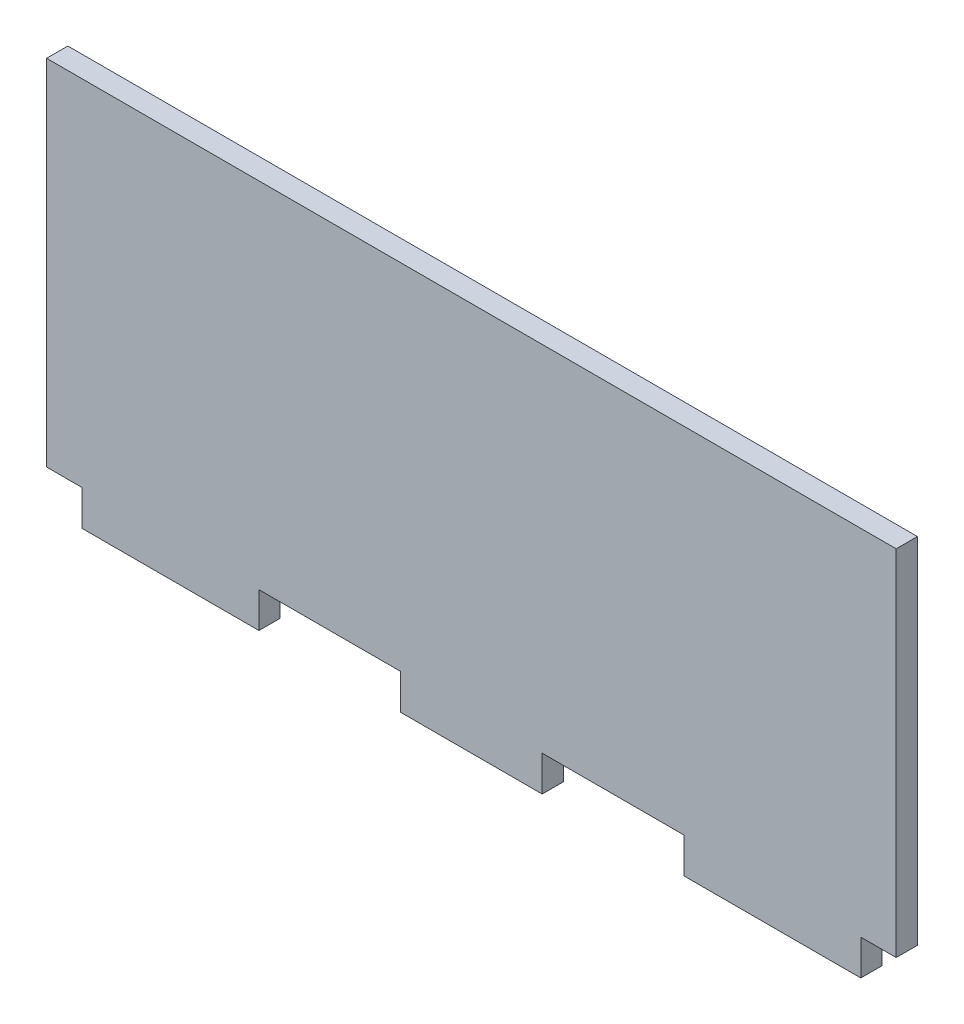
SolidWorks part; units mm, degrees
ref_plane "Plano frontal" through (0, 0, 0) normal (0, 0, 1) x (1, 0, 0)
ref_plane "Plano superior" through (0, 0, 0) normal (0, 1, 0) x (1, 0, 0)
ref_plane "Plano direito" through (0, 0, 0) normal (1, 0, 0) x (0, 0, -1)
sketch "Esboço1" plane through (0, 0, 0) normal (0, 0, 1) x (1, 0, 0)
  line L0 (-43.4908, -22.8963) -> (-23.4908, -22.8963)
  line L1 (-73.4908, 27.1037) -> (46.5092, 27.1037)
  line L2 (-73.4908, 27.1037) -> (-73.4908, -22.8963)
  line L3 (-73.4908, -22.8963) -> (-68.4908, -22.8963)
  line L4 (46.5092, 27.1037) -> (46.5092, -22.8963)
  line L5 (-3.4908, -22.8963) -> (16.5092, -22.8963)
  line L6 (-68.4908, -22.8963) -> (-68.4908, -27.8963)
  line L7 (-68.4908, -27.8963) -> (-43.4908, -27.8963)
  line L8 (-43.4908, -22.8963) -> (-43.4908, -27.8963)
  line L9 (41.5092, -22.8963) -> (46.5092, -22.8963)
  line L10 (-23.4908, -22.8963) -> (-23.4908, -27.8963)
  line L11 (-23.4908, -27.8963) -> (-3.4908, -27.8963)
  line L12 (-3.4908, -22.8963) -> (-3.4908, -27.8963)
  line L14 (16.5092, -22.8963) -> (16.5092, -27.8963)
  line L15 (16.5092, -27.8963) -> (41.5092, -27.8963)
  line L16 (41.5092, -22.8963) -> (41.5092, -27.8963)
  dimension "D1" = 120
  dimension "D2" = 50
  dimension "D3" = 5
  dimension "D4" = 25
  dimension "D5" = 5
  dimension "D6" = 5
  dimension "D7" = 5
  dimension "D8" = 20
  dimension "D9" = 20
  dimension "D10" = 25
  dimension "D11" = 5
extrude "Ressalto-extrusão1" add sketch "Esboço1" along normal blind 3
